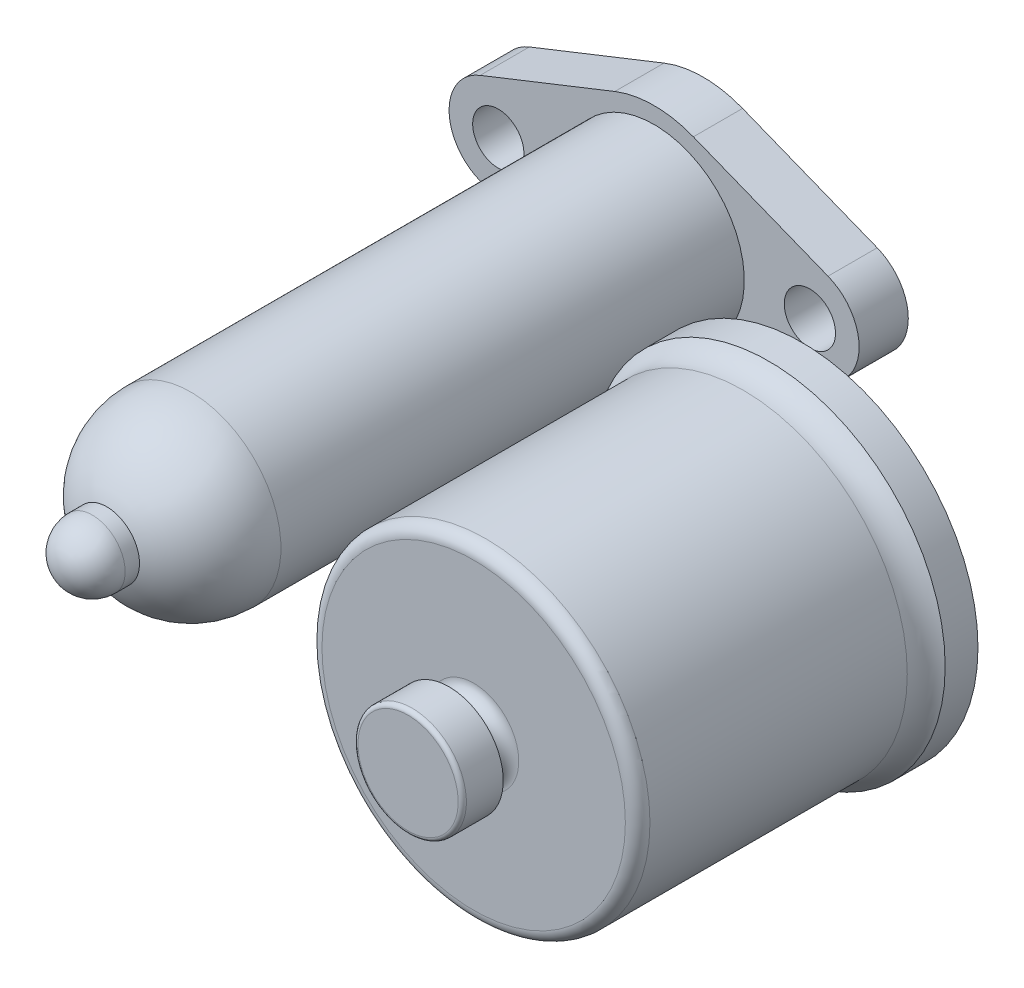
SolidWorks part; units mm, degrees
ref_plane "Front Plane" through (0, 0, 0) normal (0, 0, 1) x (1, 0, 0)
ref_plane "Top Plane" through (0, 0, 0) normal (0, 1, 0) x (1, 0, 0)
ref_plane "Right Plane" through (0, 0, 0) normal (1, 0, 0) x (0, 0, -1)
sketch "Sketch1" plane through (0, 0, 0) normal (0, 1, 0) x (1, 0, 0)
  line L0 (0, 39.8326) -> (0, -32) construction
  line L1 (22, 113) -> (22, 0)
  line L6 (16, 0) -> (16, 113)
  line L7 (16, 113) -> (22, 113)
  line L9 (4.86, -15.244) -> (4.86, -26)
  line L10 (4.86, -26) -> (0, -28.8059)
  line L11 (0, -28.8059) -> (0, -32)
  line L14 (8, -20.4939) -> (8, -24)
  arc A5 (16, 0) -> (4.86, -15.244) centre (0, 0) cw
  arc A8 (22, 0) -> (8, -20.4939) centre (0, 0) cw
  arc A10 (8, -24) -> (0, -32) centre (0, -24) cw
  dimension "D4" = 22
  dimension "D5" = 16
  dimension "D3" = 26
  dimension "D6" = 8
  dimension "D1" = 22
  dimension "D2" = 16
  dimension "D7" = 6
  dimension "D8" = 9.72
  dimension "D9" = 60
  dimension "D10" = 113
revolve "Revolve1" add sketch "Sketch1" angle 360 about L0
sketch "Sketch2" plane through (0, 0, 0) normal (0, 1, 0) x (1, 0, 0)
  line L0 (85, 126.7727) -> (85, -50.3142) construction
  line L1 (128, 64) -> (128, 56)
  line L3 (125, 49.755) -> (125, -13)
  line L4 (122, -16) -> (96, -16)
  line L5 (93, -19) -> (93, -22)
  line L6 (93, -22) -> (98.2205, -22)
  line L7 (98.2205, -22) -> (98.2205, -31)
  line L8 (97.2205, -32) -> (85, -32)
  line L9 (85, -32) -> (85, -23)
  line L10 (85, -23) -> (86.5, -23)
  line L11 (86.5, -23) -> (86.5, -14.3301)
  line L12 (86.5, -14.3301) -> (89, -10)
  line L13 (89, -10) -> (89, 4)
  line L14 (89, 4) -> (91.4914, 4)
  line L15 (93.4144, 2.5494) -> (96.5856, -8.5494)
  line L16 (98.5086, -10) -> (118, -10)
  line L17 (119, -9) -> (119, 64)
  line L18 (119, 64) -> (128, 64)
  arc A1 (125, 49.755) -> (128, 56) centre (133, 49.755) cw
  arc A2 (96, -16) -> (93, -19) centre (96, -19) ccw
  arc A3 (96.5856, -8.5494) -> (98.5086, -10) centre (98.5086, -8) ccw
  arc A4 (91.4914, 4) -> (93.4144, 2.5494) centre (91.4914, 2) cw
  arc A5 (-8, -24) -> (8, -24) centre (0, -24) ccw construction
  arc A6 (125, -13) -> (122, -16) centre (122, -13) cw
  arc A7 (119, -9) -> (118, -10) centre (118, -9) cw
  arc A8 (98.2205, -31) -> (97.2205, -32) centre (97.2205, -31) cw
  point P27 (125, 60.1365)
  point P32 (97, -10)
  point P35 (93, 4)
  point P48 (90.2457, 4)
  point P49 (89, -3)
  point P52 (125, -16)
  point P57 (98.2205, -32)
  dimension "D10" = 8
  dimension "D18" = 3
  dimension "D20" = 2
  dimension "D21" = 2
  dimension "D22" = 3
  dimension "D23" = 1
  dimension "D24" = 1
  dimension "D1" = 85
  dimension "D2" = 8
  dimension "D3" = 80
  dimension "D4" = 13.2205
  dimension "D5" = 6
  dimension "D6" = 1.5
  dimension "D7" = 16
  dimension "D8" = 9
  dimension "D9" = 6
  dimension "D11" = 6
  dimension "D12" = 30
  dimension "D13" = 14
  dimension "D14" = 8
  dimension "D15" = 86
  dimension "D16" = 68
  dimension "D17" = 24
  dimension "D19" = 16
revolve "Revolve2" add sketch "Sketch2" angle 360 about L0
ref_plane "Plane1" through (0, 0, -113) normal (0, 0, 1) x (1, 0, 0)
sketch "Sketch4" plane through (0, 0, -113) normal (0, 0, -1) x (-1, 0, 0)
  line L0 (-38, 0) -> (58.353, 0) construction
  line L1 (-42.4211, 11.1559) -> (-9.5789, 24.1711)
  line L2 (0, 43.2953) -> (0, -33.955) construction
  line L3 (42.4211, 11.1559) -> (9.5789, 24.1711)
  line L4 (42.4211, -11.1559) -> (9.5789, -24.1711)
  line L5 (-42.4211, -11.1559) -> (-9.5789, -24.1711)
  arc A0 (-9.5789, -24.1711) -> (9.5789, -24.1711) centre (0, 0) ccw
  circle A1 centre (38, 0) radius 6.25
  circle A2 centre (-38, 0) radius 6.25
  arc A3 (-42.4211, 11.1559) -> (-42.4211, -11.1559) centre (-38, 0) ccw
  arc A4 (42.4211, -11.1559) -> (42.4211, 11.1559) centre (38, 0) ccw
  arc A5 (9.5789, 24.1711) -> (-9.5789, 24.1711) centre (0, 0) ccw
  dimension "D1" = 52
  dimension "D2" = 12.5
  dimension "D3" = 24
  dimension "D4" = 12.5
  dimension "D6" = 76
extrude "Boss-Extrude1" add sketch "Sketch4" along normal blind 12 contours L4 A0 L5 A3 L1 A5 L3 A4
sketch "Sketch6" plane through (0, 0, -125) normal (0, 0, -1) x (-1, 0, 0)
  line L4 (42.4211, 11.1559) -> (9.5789, 24.1711)
  line L5 (-9.5789, 24.1711) -> (-42.4211, 11.1559)
  line L6 (-42.4211, -11.1559) -> (-9.5789, -24.1711)
  line L7 (9.5789, -24.1711) -> (42.4211, -11.1559)
  line L8 (42.4211, 11.1559) -> (9.5789, 24.1711)
  line L9 (-9.5789, 24.1711) -> (-42.4211, 11.1559)
  line L10 (-42.4211, -11.1559) -> (-9.5789, -24.1711)
  line L11 (9.5789, -24.1711) -> (42.4211, -11.1559)
  circle A0 centre (0, 0) radius 22 construction
  circle A1 centre (0, 0) radius 22
  arc A4 (42.4211, -11.1559) -> (42.4211, 11.1559) centre (38, 0) ccw
  arc A5 (9.5789, 24.1711) -> (-9.5789, 24.1711) centre (0, 0) ccw
  arc A6 (-42.4211, 11.1559) -> (-42.4211, -11.1559) centre (-38, 0) ccw
  arc A7 (-9.5789, -24.1711) -> (9.5789, -24.1711) centre (0, 0) ccw
  arc A8 (42.4211, -11.1559) -> (42.4211, 11.1559) centre (38, 0) ccw
  arc A9 (9.5789, 24.1711) -> (-9.5789, 24.1711) centre (0, 0) ccw
  arc A10 (-42.4211, 11.1559) -> (-42.4211, -11.1559) centre (-38, 0) ccw
  arc A11 (-9.5789, -24.1711) -> (9.5789, -24.1711) centre (0, 0) ccw
  dimension "D1" = 0
sketch "Sketch7" plane through (0, 0, -125) normal (0, 0, -1) x (-1, 0, 0)
  circle A0 centre (0, 0) radius 16
  circle A1 centre (-38, 0) radius 6.25
  circle A2 centre (38, 0) radius 6.25
  dimension "D1" = 12.5
  dimension "D2" = 12.5
  dimension "D3" = 32
extrude "Cut-Extrude2" cut sketch "Sketch7" against normal blind 32 contours A2 | A0 | A1
sketch "Sketch11" plane through (0, 0, -64) normal (0, 0, -1) x (-1, 0, 0)
  line L0 (118.3498, 0) -> (-157.5553, 0) construction
  circle A0 centre (-85, 0) radius 38 construction
  circle A1 centre (-123, 0) radius 2
  dimension "D1" = 76
  dimension "D2" = 4
extrude "Cut-Extrude3" cut sketch "Sketch11" against normal blind 8
pattern_circular "CirPattern6" count 4 over 360 about axis through (85, 0, 0) along (0, 0, 1) of "Cut-Extrude3"
sketch "Sketch12" plane through (0, 0, 0) normal (1, 0, 0) x (0, 0, -1)
  line L0 (144.5165, 0) -> (-74.0491, 0) construction
